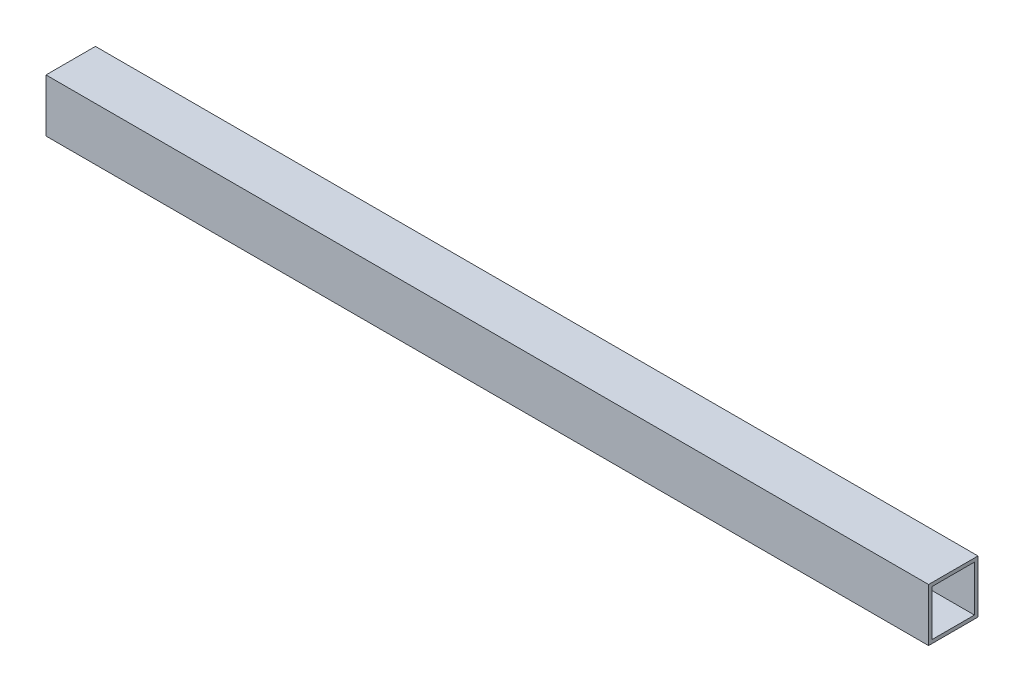
SolidWorks part; units mm, degrees
ref_plane "Спереди" through (0, 0, 0) normal (0, 0, 1) x (1, 0, 0)
ref_plane "Сверху" through (0, 0, 0) normal (0, 1, 0) x (1, 0, 0)
ref_plane "Справа" through (0, 0, 0) normal (1, 0, 0) x (0, 0, -1)
sketch "Эскиз2" plane through (0, 0, 0) normal (1, 0, 0) x (0, 0, -1)
  line L1 (-35, 37.5) -> (35, 37.5)
  line L2 (-35, 37.5) -> (-35, -37.5)
  line L3 (-35, -37.5) -> (35, -37.5)
  line L4 (35, 37.5) -> (35, -37.5)
  line L5 (-35, 37.5) -> (35, -37.5) construction
  line L6 (-35, -37.5) -> (35, 37.5) construction
  point P0 (0, 0)
extrude "Вытянуть-Тонкостенный1" add sketch "Эскиз2" along normal blind 1250 thin
